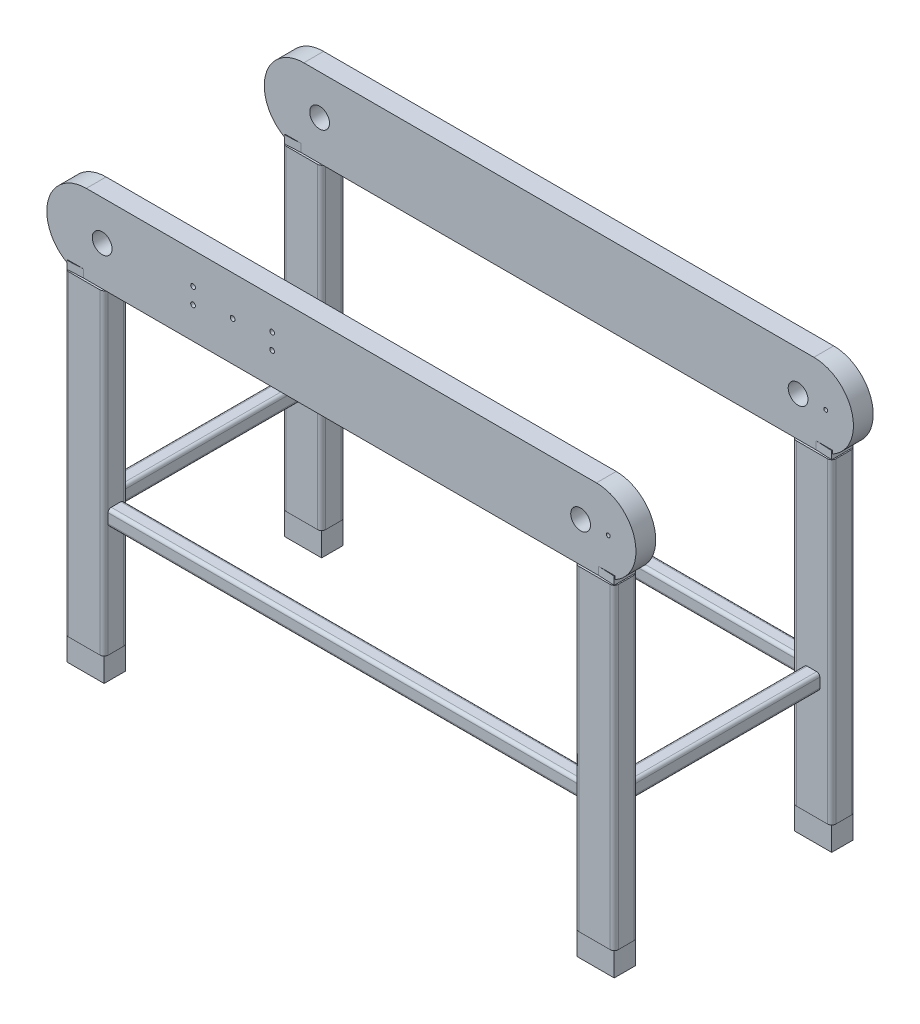
SolidWorks part; units mm, degrees
ref_plane "Front Plane" through (0, 0, 0) normal (0, 0, 1) x (1, 0, 0)
ref_plane "Top Plane" through (0, 0, 0) normal (0, 1, 0) x (1, 0, 0)
ref_plane "Right Plane" through (0, 0, 0) normal (1, 0, 0) x (0, 0, -1)
sketch "Sketch2" plane through (0, 0, 0) normal (0, 0, 1) x (1, 0, 0)
  circle A0 centre (-9.3798, 0) radius 25
  circle A2 centre (45.6202, 0) radius 25
  circle A3 centre (45.6202, 0) radius 12.5
  circle A4 centre (100.6202, 0) radius 25
  circle A5 centre (100.6202, 0) radius 12.5
  circle A6 centre (155.6202, 0) radius 25
  circle A7 centre (155.6202, 0) radius 12.5
  circle A8 centre (210.6202, 0) radius 25
  circle A9 centre (210.6202, 0) radius 12.5
  circle A10 centre (265.6202, 0) radius 25
  circle A11 centre (265.6202, 0) radius 12.5
  circle A12 centre (320.6202, 0) radius 25
  circle A13 centre (320.6202, 0) radius 12.5
  circle A14 centre (375.6202, 0) radius 25
  circle A15 centre (375.6202, 0) radius 12.5
  circle A16 centre (430.6202, 0) radius 25
  circle A17 centre (430.6202, 0) radius 12.5
  circle A18 centre (485.6202, 0) radius 25
  circle A19 centre (485.6202, 0) radius 12.5
  circle A20 centre (540.6202, 0) radius 25
  circle A21 centre (540.6202, 0) radius 12.5
  circle A22 centre (595.6202, 0) radius 25
  circle A26 centre (-9.3798, 0) radius 12.5
  circle A27 centre (595.6202, 0) radius 12.5
  circle A28 centre (595.6202, 0) radius 12.5
  dimension "D1" = 50
  dimension "D4" = 3
  dimension "D3" = 10
sketch "Sketch4" plane through (0, 0, 0) normal (0, 0, 1) x (1, 0, 0)
  line L0 (-29.3798, 0) -> (615.6202, 0) construction
  line L1 (-29.3798, 50) -> (615.6202, 50)
  line L2 (-29.3798, -50) -> (615.6202, -50)
  arc A0 (-29.3798, 50) -> (-29.3798, -50) centre (-29.3798, 0) ccw
  arc A1 (615.6202, -50) -> (615.6202, 50) centre (615.6202, 0) ccw
  circle A2 centre (-9.3798, 0) radius 25 construction
  circle A3 centre (595.6202, 0) radius 25 construction
  circle A4 centre (-9.3798, 0) radius 12.5
  circle A5 centre (595.6202, 0) radius 12.5
  point P3 (293.1202, 0)
  dimension "D1" = 20
  dimension "D2" = 20
  dimension "D3" = 50
extrude "Boss-Extrude3" add sketch "Sketch4" along normal blind 25 from offset 125
mirror "Mirror8" about plane through (0, 0, 0) normal (0, 0, 1) of bodies 107
sketch3d "3DSketch1"
  line L0 (-29.3798, -50, 137.5) -> (-29.3798, -450, 137.5)
  line L1 (-29.3798, -50, 150) -> (-29.3798, -50, 125) construction
  line L2 (615.6202, -50, 137.5) -> (615.6202, -450, 137.5)
  line L3 (615.6202, -50, 150) -> (615.6202, -50, 125) construction
  line L4 (615.6202, -50, -137.5) -> (615.6202, -450, -137.5)
  line L5 (615.6202, -50, -150) -> (615.6202, -50, -125) construction
  line L6 (-29.3798, -50, -137.5) -> (-29.3798, -450, -137.5)
  line L7 (-29.3798, -50, -150) -> (-29.3798, -50, -125) construction
  dimension "D1" = 400
  dimension "D2" = 400
  dimension "D3" = 400
  dimension "D4" = 400
other "Rectangular tube - configured 50 X 30 X 2.6(1)"
ref_plane "Plane1" through (-29.3798, -50, -137.5) normal (0, -1, 0) x (0, 0, -1)
sketch "Sketch13" plane through (-29.3798, -50, -137.5) normal (0, -1, 0) x (0, 0, -1)
  line L0 (-9.8, -22.4) -> (9.8, -22.4)
  line L1 (-12.4, -19.8) -> (-12.4, 19.8)
  line L2 (9.8, 22.4) -> (-9.8, 22.4)
  line L3 (12.4, 19.8) -> (12.4, -19.8)
  line L4 (-9.8, -25) -> (9.8, -25)
  line L5 (-15, -19.8) -> (-15, 19.8)
  line L6 (9.8, 25) -> (-9.8, 25)
  line L7 (15, 19.8) -> (15, -19.8)
  arc A0 (15, 19.8) -> (9.8, 25) centre (9.8, 19.8) ccw
  arc A1 (9.8, -25) -> (15, -19.8) centre (9.8, -19.8) ccw
  arc A2 (-15, -19.8) -> (-9.8, -25) centre (-9.8, -19.8) ccw
  arc A3 (-9.8, 25) -> (-15, 19.8) centre (-9.8, 19.8) ccw
  arc A4 (-9.8, 22.4) -> (-12.4, 19.8) centre (-9.8, 19.8) ccw
  arc A5 (12.4, 19.8) -> (9.8, 22.4) centre (9.8, 19.8) ccw
  arc A6 (9.8, -22.4) -> (12.4, -19.8) centre (9.8, -19.8) ccw
  arc A7 (-12.4, -19.8) -> (-9.8, -22.4) centre (-9.8, -19.8) ccw
  point P0 (0, 25)
  point P1 (15, 0)
  point P2 (0, -25)
  point P3 (-15, 0)
  point P4 (-15, 25)
  point P5 (15, 25)
  point P6 (15, -25)
  point P7 (-15, -25)
  point P8 (0, 0)
  point P33 (0, 0)
  dimension "D1" = 5.2
  dimension "Thickness" = 2.6
  dimension "V_leg" = 50
  dimension "H_leg" = 30
sketch3d "3DSketch2"
  line L0 (639.0971, -50, 150.977) -> (639.0971, -50, 124.023)
  line L1 (639.0971, -50, 124.023) -> (616.3681, -50, 125.1)
  line L2 (595.8202, -50, 125.1) -> (635.4202, -50, 125.1) construction
  line L3 (616.3681, -50, 125.1) -> (616.3681, -50, 149.9)
  line L4 (635.4202, -50, 149.9) -> (595.8202, -50, 149.9) construction
  line L5 (616.3681, -50, 149.9) -> (639.0971, -50, 150.977)
  arc A0 (640.6202, -50, 147.3) -> (635.4202, -50, 152.5) centre (635.4202, -50, 147.3) ccw construction
  arc A1 (635.4202, -50, 122.5) -> (640.6202, -50, 127.7) centre (635.4202, -50, 127.7) ccw construction
  point P5 (635.4202, -55.2, 147.3)
  point P9 (635.4202, -55.2, 127.7)
extrude "Boss-Extrude6" add sketch "3DSketch2" along direction (0, 1, 0) on the side against the normal blind 10 separate body contours L0 L1 L3 L5
pattern_linear "LPattern2" count 2 spacing 275 along (0, 0, -1) of "Boss-Extrude6"
sketch3d "3DSketch8"
  line L0 (-52.8568, -50, -150.977) -> (-52.8568, -50, -124.023)
  line L1 (-52.8568, -50, -124.023) -> (-30.6338, -50, -125.1)
  line L2 (-9.5798, -50, -125.1) -> (-49.1798, -50, -125.1) construction
  line L3 (-30.6338, -50, -125.1) -> (-30.6338, -50, -149.4368)
  line L4 (-30.6338, -50, -149.4368) -> (-52.8568, -50, -150.977)
  arc A0 (-54.3798, -50, -147.3) -> (-49.1798, -50, -152.5) centre (-49.1798, -50, -147.3) ccw construction
  arc A1 (-49.1798, -50, -122.5) -> (-54.3798, -50, -127.7) centre (-49.1798, -50, -127.7) ccw construction
  point P5 (-49.1798, -55.2, -147.3)
  point P9 (-49.1798, -55.2, -127.7)
extrude "Boss-Extrude7" add sketch "3DSketch8" along direction (0, -1, 0) on the side against the normal blind 10 separate body
sketch3d "3DSketch10"
  line L4 (-4.3798, -300, -137.5) -> (590.6202, -300, -137.5)
  line L7 (590.6202, -300, 137.5) -> (-4.3798, -300, 137.5)
  line L10 (615.6202, -300, -122.5) -> (615.6202, -300, 122.5)
  line L13 (-29.3798, -300, -122.5) -> (-29.3798, -300, 122.5)
other "Square tube - configured 20 X 20 X 2(3)"
ref_plane "Plane5" through (-4.3798, -300, -137.5) normal (1, 0, 0) x (0, 0, -1)
sketch "Sketch1" plane through (-4.3798, -300, -137.5) normal (1, 0, 0) x (0, 0, -1)
  line L0 (-6, -8) -> (6, -8)
  line L1 (-8, -6) -> (-8, 6)
  line L2 (6, 8) -> (-6, 8)
  line L3 (8, 6) -> (8, -6)
  line L4 (-6, -10) -> (6, -10)
  line L5 (-10, -6) -> (-10, 6)
  line L6 (6, 10) -> (-6, 10)
  line L7 (10, 6) -> (10, -6)
  arc A0 (10, 6) -> (6, 10) centre (6, 6) ccw
  arc A1 (6, -10) -> (10, -6) centre (6, -6) ccw
  arc A2 (-10, -6) -> (-6, -10) centre (-6, -6) ccw
  arc A3 (-6, 10) -> (-10, 6) centre (-6, 6) ccw
  arc A4 (-6, 8) -> (-8, 6) centre (-6, 6) ccw
  arc A5 (8, 6) -> (6, 8) centre (6, 6) ccw
  arc A6 (6, -8) -> (8, -6) centre (6, -6) ccw
  arc A7 (-8, -6) -> (-6, -8) centre (-6, -6) ccw
  point P0 (-10, 0)
  point P1 (10, 0)
  point P2 (0, 10)
  point P3 (0, -10)
  point P4 (0, 0)
  point P5 (-10, -10)
  point P6 (10, -10)
  point P7 (10, 10)
  point P8 (-10, 10)
  point P33 (0, 0)
  dimension "D1" = 4
  dimension "Thickness" = 2
  dimension "V_leg" = 20
other "Square tube - configured 20 X 20 X 2(4)"
ref_plane "Plane6" through (-29.3798, -300, -122.5) normal (0, 0, 1) x (1, 0, 0)
sketch "Sketch116" plane through (-29.3798, -300, -122.5) normal (0, 0, 1) x (1, 0, 0)
  line L0 (-6, -8) -> (6, -8)
  line L1 (-8, -6) -> (-8, 6)
  line L2 (6, 8) -> (-6, 8)
  line L3 (8, 6) -> (8, -6)
  line L4 (-6, -10) -> (6, -10)
  line L5 (-10, -6) -> (-10, 6)
  line L6 (6, 10) -> (-6, 10)
  line L7 (10, 6) -> (10, -6)
  arc A0 (10, 6) -> (6, 10) centre (6, 6) ccw
  arc A1 (6, -10) -> (10, -6) centre (6, -6) ccw
  arc A2 (-10, -6) -> (-6, -10) centre (-6, -6) ccw
  arc A3 (-6, 10) -> (-10, 6) centre (-6, 6) ccw
  arc A4 (-6, 8) -> (-8, 6) centre (-6, 6) ccw
  arc A5 (8, 6) -> (6, 8) centre (6, 6) ccw
  arc A6 (6, -8) -> (8, -6) centre (6, -6) ccw
  arc A7 (-8, -6) -> (-6, -8) centre (-6, -6) ccw
  point P0 (-10, 0)
  point P1 (10, 0)
  point P2 (0, 10)
  point P3 (0, -10)
  point P4 (0, 0)
  point P5 (-10, -10)
  point P6 (10, -10)
  point P7 (10, 10)
  point P8 (-10, 10)
  point P33 (0, 0)
  dimension "D1" = 4
  dimension "Thickness" = 2
  dimension "V_leg" = 20
pattern_linear "LPattern3" count 2 spacing 275 along (0, 0, 1) of "Boss-Extrude7"
combine bodies "Combine1" operation type add bodies to combine 109 146 144
combine bodies "Combine2" operation type add bodies to combine 107 157 134
sketch3d "3DSketch12"
  line L1 (-52.8568, -450, 124.023) -> (-52.8568, -450, 150.977)
  line L2 (-52.8568, -450, 124.023) -> (-5.9029, -450, 124.023)
  line L3 (-5.9029, -450, 124.023) -> (-5.9029, -450, 150.977)
  line L4 (-52.8568, -450, 150.977) -> (-5.9029, -450, 150.977)
  line L5 (-52.8568, -450, 124.023) -> (-5.9029, -450, 150.977) construction
  line L6 (-5.9029, -450, 124.023) -> (-52.8568, -450, 150.977) construction
  line L7 (639.0971, -450, 124.023) -> (639.0971, -450, 150.977)
  line L8 (639.0971, -450, 124.023) -> (592.1432, -450, 124.023)
  line L9 (592.1432, -450, 124.023) -> (592.1432, -450, 150.977)
  line L10 (639.0971, -450, 150.977) -> (592.1432, -450, 150.977)
  line L11 (639.0971, -450, 124.023) -> (592.1432, -450, 150.977) construction
  line L12 (592.1432, -450, 124.023) -> (639.0971, -450, 150.977) construction
  line L13 (639.0971, -450, -150.977) -> (639.0971, -450, -124.023)
  line L14 (639.0971, -450, -150.977) -> (592.1432, -450, -150.977)
  line L15 (592.1432, -450, -150.977) -> (592.1432, -450, -124.023)
  line L16 (639.0971, -450, -124.023) -> (592.1432, -450, -124.023)
  line L17 (639.0971, -450, -150.977) -> (592.1432, -450, -124.023) construction
  line L18 (592.1432, -450, -150.977) -> (639.0971, -450, -124.023) construction
  line L19 (-5.9029, -450, -150.977) -> (-5.9029, -450, -124.023)
  line L20 (-5.9029, -450, -150.977) -> (-52.8568, -450, -150.977)
  line L21 (-52.8568, -450, -150.977) -> (-52.8568, -450, -124.023)
  line L22 (-5.9029, -450, -124.023) -> (-52.8568, -450, -124.023)
  line L23 (-5.9029, -450, -150.977) -> (-52.8568, -450, -124.023) construction
  line L24 (-52.8568, -450, -150.977) -> (-5.9029, -450, -124.023) construction
  arc A0 (-4.3798, -450, 147.3) -> (-9.5798, -450, 152.5) centre (-9.5798, -450, 147.3) ccw construction
  arc A1 (595.8202, -450, 152.5) -> (590.6202, -450, 147.3) centre (595.8202, -450, 147.3) ccw construction
  arc A2 (595.8202, -450, -122.5) -> (590.6202, -450, -127.7) centre (595.8202, -450, -127.7) ccw construction
  arc A3 (-49.1798, -450, -122.5) -> (-54.3798, -450, -127.7) centre (-49.1798, -450, -127.7) ccw construction
  point P0 (-29.3798, -450, 137.5)
  point P9 (-9.5798, -455.2, 147.3)
  point P10 (615.6202, -450, 137.5)
  point P19 (595.8202, -455.2, 147.3)
  point P20 (615.6202, -450, -137.5)
  point P29 (595.8202, -455.2, -127.7)
  point P30 (-29.3798, -450, -137.5)
  point P39 (-49.1798, -455.2, -127.7)
sketch "Sketch117" plane through (0, 0, 150) normal (0, 0, 1) x (1, 0, 0)
  line L1 (205.6202, 10) -> (105.6202, 10)
  line L2 (205.6202, 10) -> (205.6202, -10)
  line L3 (205.6202, -10) -> (105.6202, -10)
  line L4 (105.6202, 10) -> (105.6202, -10)
  line L5 (205.6202, 10) -> (105.6202, -10) construction
  line L6 (205.6202, -10) -> (105.6202, 10) construction
  circle A1 centre (105.6202, 10) radius 3
  circle A2 centre (205.6202, 10) radius 3
  circle A3 centre (105.6202, -10) radius 3
  circle A4 centre (205.6202, -10) radius 3
  circle A5 centre (155.6202, 0) radius 3
  point P0 (155.6202, 0)
  dimension "D3" = 6
  dimension "D4" = 6
  dimension "D5" = 6
  dimension "D6" = 6
  dimension "D7" = 6
  dimension "D1" = 100
  dimension "D2" = 20
sketch "Sketch119" plane through (0, 0, -150) normal (0, 0, -1) x (-1, 0, 0)
  line L1 (-105.6202, -9.8395) -> (-205.6202, -9.8395)
  line L2 (-105.6202, -9.8395) -> (-105.6202, 10.1605)
  line L3 (-105.6202, 10.1605) -> (-205.6202, 10.1605)
  line L4 (-205.6202, -9.8395) -> (-205.6202, 10.1605)
  line L5 (-105.6202, -9.8395) -> (-205.6202, 10.1605) construction
  line L6 (-105.6202, 10.1605) -> (-205.6202, -9.8395) construction
  circle A2 centre (-155.6202, 0.1605) radius 3
  circle A5 centre (-205.6202, 10.1605) radius 3
  circle A6 centre (-205.6202, -9.8395) radius 3
  circle A7 centre (-105.6202, 10.1605) radius 3
  circle A8 centre (-105.6202, -9.8395) radius 3
  point P0 (-155.6202, 0)
  dimension "D2" = 6
  dimension "D3" = 6
  dimension "D1" = 20
extrude "Cut-Extrude1" cut sketch "Sketch117" against normal blind 10 contours L2 A2 L1 | L1 A2 L2 | A1 | A3 | A5 | A4
extrude "Cut-Extrude2" cut sketch "Sketch119" against normal blind 5 contours A5 | A6 | A8 | A2 | A7
extrude "Boss-Extrude8" add sketch "3DSketch12" along direction (0, 1, 0) on the side of the normal blind 30 separate body contours L3 L4 L1 L2 | L19 L22 L21 L20 | L7 L10 L9 L8 | L13 L16 L15 L14
sketch "Sketch120" plane through (0, 0, 125) normal (0, 0, -1) x (-1, 0, 0)
  line L0 (-665.6202, 0) -> (-630.6202, 0)
  arc A0 (-615.6202, 50) -> (-639.0971, -44.1456) centre (-615.6202, 0) ccw construction
  arc A1 (-615.6202, 50) -> (-639.0971, -44.1456) centre (-615.6202, 0) ccw construction
  circle A2 centre (-630.6202, 0) radius 2.5
  dimension "D2" = 5
  dimension "D1" = 35
extrude "Cut-Extrude3" cut sketch "Sketch120" against normal mid plane 929 contours A2
